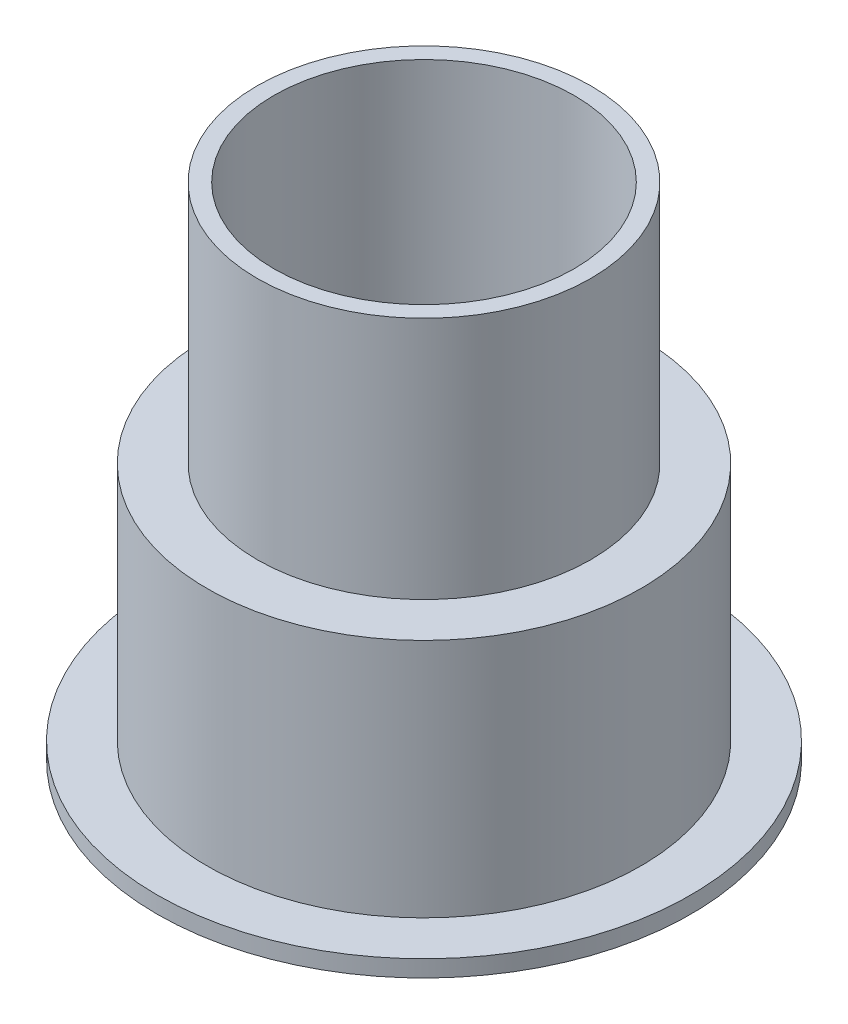
SolidWorks part; units mm, degrees
ref_plane "Front Plane" through (0, 0, 0) normal (0, 0, 1) x (1, 0, 0)
ref_plane "Top Plane" through (0, 0, 0) normal (0, 1, 0) x (1, 0, 0)
ref_plane "Right Plane" through (0, 0, 0) normal (1, 0, 0) x (0, 0, -1)
sketch "Sketch1" plane through (0, 0, 0) normal (0, 0, 1) x (1, 0, 0)
  line L0 (0, 0) -> (0, 13.5207) construction
  line L1 (6, -0.8548) -> (6, 6.1452)
  line L2 (6, 6.1452) -> (0, 6.1452)
  line L3 (4.5, 6.8452) -> (4.5, 14.1452)
  line L4 (6, -0.8548) -> (8, -0.8548)
  line L5 (5, 6.8452) -> (5, 14.1452)
  line L6 (6.5, -0.3548) -> (8, -0.3548)
  line L7 (6.5, -0.3548) -> (6.5, 6.8452)
  line L8 (6.5, 6.8452) -> (5, 6.8452)
  line L9 (0, 6.8452) -> (0, 6.1452)
  line L10 (4.5, 14.1452) -> (5, 14.1452)
  line L11 (8, -0.8548) -> (8, -0.3548)
  line L12 (4.5, 6.1452) -> (4.5, 14.1452) construction
  line L13 (4.5, 6.8452) -> (0, 6.8452)
  line L15 (5, 6.1452) -> (5, 14.1452) construction
  dimension "D1" = 6
  dimension "D2" = 2
  dimension "D3" = 7
  dimension "D4" = 0.7
  dimension "D5" = 1.5
  dimension "D7" = 0.5
  dimension "D8" = 0.5
  dimension "D6" = 0.5
revolve "Revolve1" add sketch "Sketch1" angle 360 about L0
